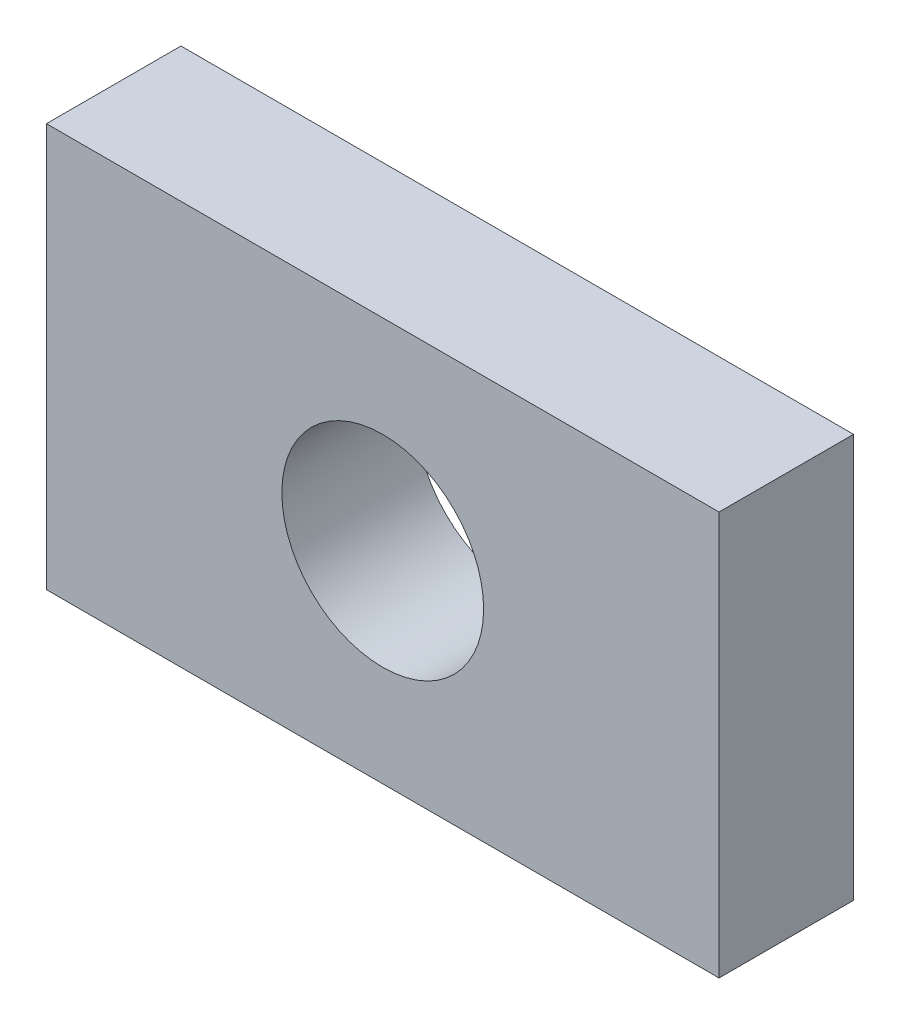
SolidWorks part; units mm, degrees
material "Acrylic (Medium-high impact)"
ref_plane "Front Plane" through (0, 0, 0) normal (0, 0, 1) x (1, 0, 0)
ref_plane "Top Plane" through (0, 0, 0) normal (0, 1, 0) x (1, 0, 0)
ref_plane "Right Plane" through (0, 0, 0) normal (1, 0, 0) x (0, 0, -1)
sketch "Model" plane through (0, 0, 0) normal (0, 0, 1) x (1, 0, 0)
  line L251 (-5, 3) -> (-5, -3)
  line L252 (-5, 3) -> (5, 3)
  line L253 (5, 3) -> (5, -3)
  line L254 (5, -3) -> (-5, -3)
  circle A105 centre (0, 0) radius 1.5
  dimension "D1" = 3
  dimension "D2" = 5
  dimension "D3" = 5
  dimension "D4" = 3
  dimension "D5" = 3
extrude "Boss-Extrude1" add sketch "Model" along normal blind 2
